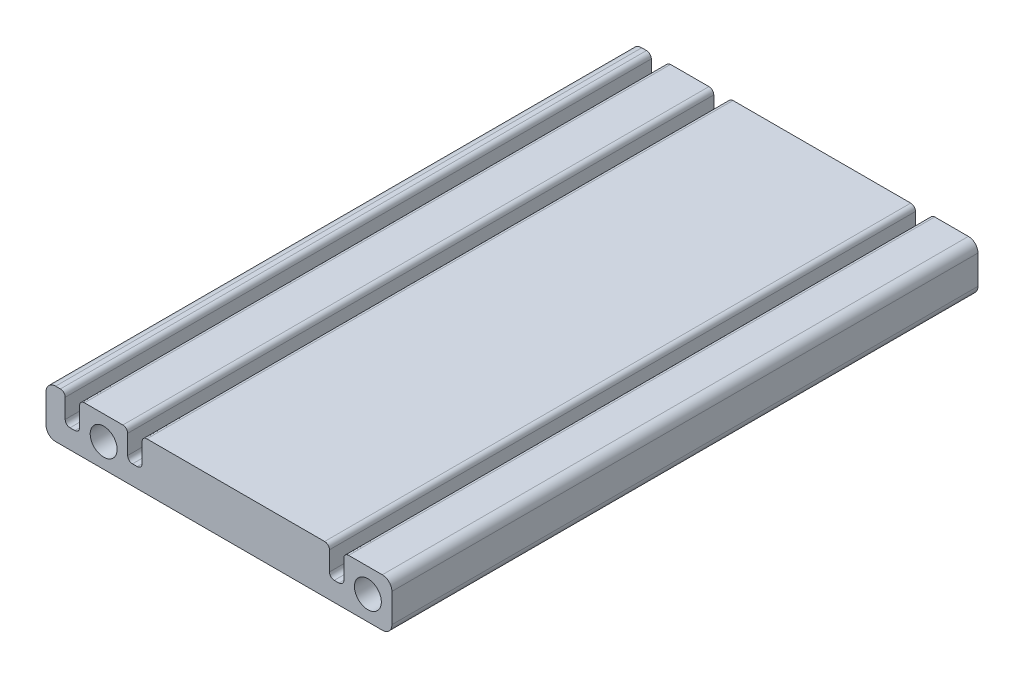
SolidWorks part; units mm, degrees
ref_plane "Plan de face" through (0, 0, 0) normal (0, 0, 1) x (1, 0, 0)
ref_plane "Plan de dessus" through (0, 0, 0) normal (0, 1, 0) x (1, 0, 0)
ref_plane "Plan de droite" through (0, 0, 0) normal (1, 0, 0) x (0, 0, -1)
sketch "Esquisse1" plane through (0, 0, 0) normal (0, 0, 1) x (1, 0, 0)
  line L0 (-35.8911, -3.0896) -> (-35.8911, 6.9104)
  line L1 (-35.8911, 6.9104) -> (-31.8911, 6.9104)
  line L2 (-31.8911, 6.9104) -> (-31.8911, 0.9104)
  line L3 (-31.8911, 0.9104) -> (-28.8911, 0.9104)
  line L4 (-28.8911, 0.9104) -> (-28.8911, 6.9104)
  line L5 (-28.8911, 6.9104) -> (-18.8911, 6.9104)
  line L6 (-18.8911, 6.9104) -> (-18.8911, 0.9104)
  line L7 (-18.8911, 0.9104) -> (-15.8911, 0.9104)
  line L8 (-15.8911, 0.9104) -> (-15.8911, 6.9104)
  line L9 (-15.8911, 6.9104) -> (23.1089, 6.9104)
  line L10 (23.1089, 6.9104) -> (23.1089, 0.9104)
  line L11 (23.1089, 0.9104) -> (26.1089, 0.9104)
  line L12 (26.1089, 0.9104) -> (26.1089, 6.9104)
  line L13 (26.1089, 6.9104) -> (36.1089, 6.9104)
  line L14 (36.1089, 6.9104) -> (36.1089, -3.0896)
  line L15 (36.1089, -3.0896) -> (-35.8911, -3.0896)
  line L16 (-23.8911, 6.9104) -> (-23.8911, -3.0896) construction
  line L17 (31.1089, 6.9104) -> (31.1089, -3.0896) construction
  circle A0 centre (-23.8911, 1.9104) radius 2.8
  circle A1 centre (31.1089, 1.9104) radius 2.8
  dimension "D7" = 5.6
  dimension "D1" = 10
  dimension "D2" = 4
  dimension "D3" = 3
  dimension "D4" = 10
  dimension "D5" = 39
  dimension "D6" = 4
extrude "Boss.-Extru.1" add sketch "Esquisse1" along normal blind 122 contours A1 | A0 | L4 L5 L6 L7 L8 L9 L10 L11 L12 L13 L14 L15 L0 L1 L2 L3
fillet "Congé1" radius 1 12 edges at (26.1089, 6.9104, 61) (26.1089, 0.9104, 61) (23.1089, 6.9104, 61) (-15.8911, 0.9104, 61) (-15.8911, 6.9104, 61) (-18.8911, 6.9104, 61) (-28.8911, 6.9104, 61) (-28.8911, 0.9104, 61) (-31.8911, 6.9104, 61) (-31.8911, 0.9104, 61) (-18.8911, 0.9104, 61) (23.1089, 0.9104, 61)
fillet "Congé2" radius 2 4 edges at (-35.8911, -3.0896, 61) (-35.8911, 6.9104, 61) (36.1089, 6.9104, 61) (36.1089, -3.0896, 61)
